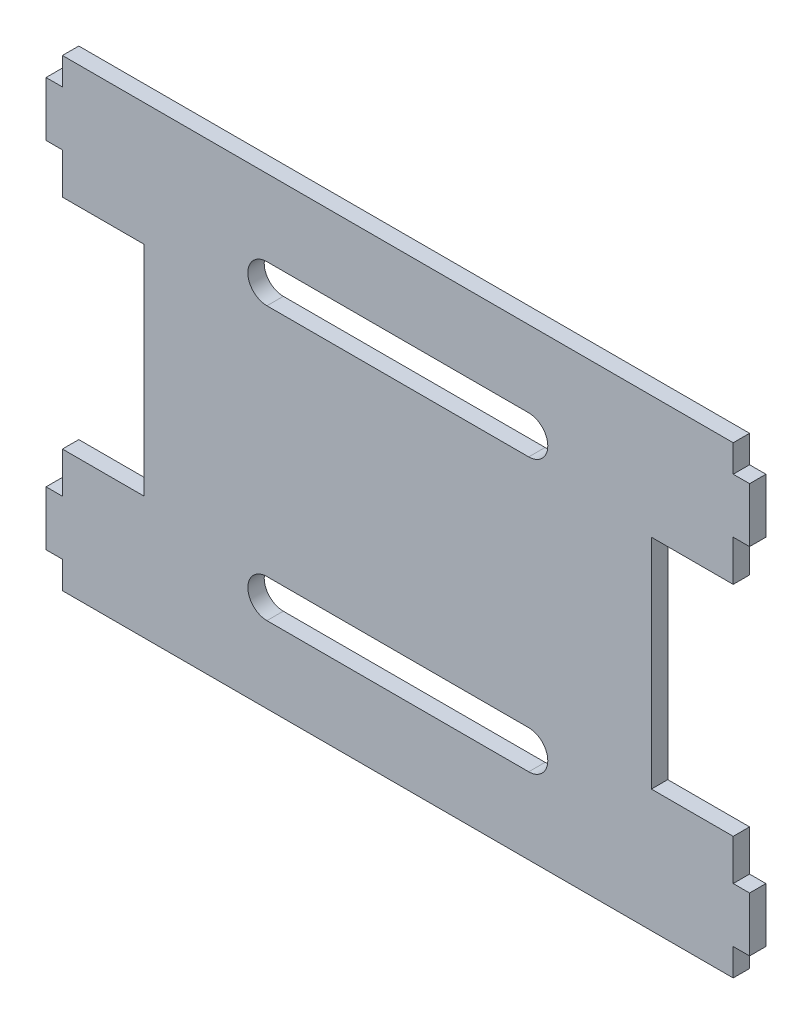
SolidWorks part; units mm, degrees
ref_plane "Front Plane" through (0, 0, 0) normal (0, 0, 1) x (1, 0, 0)
ref_plane "Top Plane" through (0, 0, 0) normal (0, 1, 0) x (1, 0, 0)
ref_plane "Right Plane" through (0, 0, 0) normal (1, 0, 0) x (0, 0, -1)
sketch "Sketch1" plane through (0, 0, 0) normal (0, 0, 1) x (1, 0, 0)
  line L0 (-61.5, 27.5) -> (-61.5, 20)
  line L1 (-61.5, 42.5) -> (61.5, 42.5)
  line L2 (-61.5, 42.5) -> (-61.5, 37.5)
  line L3 (-61.5, -42.5) -> (61.5, -42.5)
  line L4 (61.5, 42.5) -> (61.5, 37.5)
  line L5 (-61.5, 42.5) -> (61.5, -42.5) construction
  line L6 (-61.5, -42.5) -> (61.5, 42.5) construction
  line L7 (-64.5, 37.5) -> (-61.5, 37.5)
  line L8 (-64.5, 37.5) -> (-64.5, 27.5)
  line L9 (-64.5, 27.5) -> (-61.5, 27.5)
  line L11 (61.5, 27.5) -> (61.5, 20)
  line L12 (61.5, -20) -> (61.5, -27.5)
  line L13 (61.5, -37.5) -> (61.5, -42.5)
  line L14 (-64.5, -37.5) -> (-61.5, -37.5)
  line L15 (-64.5, -27.5) -> (-64.5, -37.5)
  line L16 (-64.5, -27.5) -> (-61.5, -27.5)
  line L20 (61.5, -37.5) -> (64.5, -37.5)
  line L22 (61.5, -27.5) -> (64.5, -27.5)
  line L23 (64.5, -27.5) -> (64.5, -37.5)
  line L26 (61.5, 27.5) -> (64.5, 27.5)
  line L28 (61.5, 37.5) -> (64.5, 37.5)
  line L29 (64.5, 37.5) -> (64.5, 27.5)
  line L30 (-24, -25) -> (24, -25) construction
  line L31 (-61.5, 20) -> (-46.5, 20)
  line L33 (-61.5, -20) -> (-46.5, -20)
  line L34 (-46.5, 20) -> (-46.5, -20)
  line L35 (-61.5, -37.5) -> (-61.5, -42.5)
  line L37 (61.5, -20) -> (46.5, -20)
  line L38 (46.5, 20) -> (46.5, -20)
  line L39 (61.5, 20) -> (46.5, 20)
  line L40 (-24, 25) -> (24, 25) construction
  line L43 (-24, 28.5) -> (24, 28.5)
  line L44 (-24, 21.5) -> (24, 21.5)
  line L45 (-24, -21.5) -> (24, -21.5)
  line L46 (-24, -28.5) -> (24, -28.5)
  line L47 (-61.5, -20) -> (-61.5, -27.5)
  arc A2 (-24, 28.5) -> (-24, 21.5) centre (-24, 25) ccw
  arc A3 (24, 21.5) -> (24, 28.5) centre (24, 25) ccw
  arc A4 (-24, -21.5) -> (-24, -28.5) centre (-24, -25) ccw
  arc A5 (24, -28.5) -> (24, -21.5) centre (24, -25) ccw
  point P0 (0, 0)
  point P6 (-61.5, 32.5)
  point P24 (-54, 0)
  point P29 (0, 0)
  point P30 (0, 0)
  point P36 (0, 25)
  point P41 (0, 0)
  point P42 (0, 0)
  point P45 (0, -25)
  dimension "D1" = 123
  dimension "D2" = 85
extrude "Boss-Extrude3" add sketch "Sketch1" along normal blind 3
